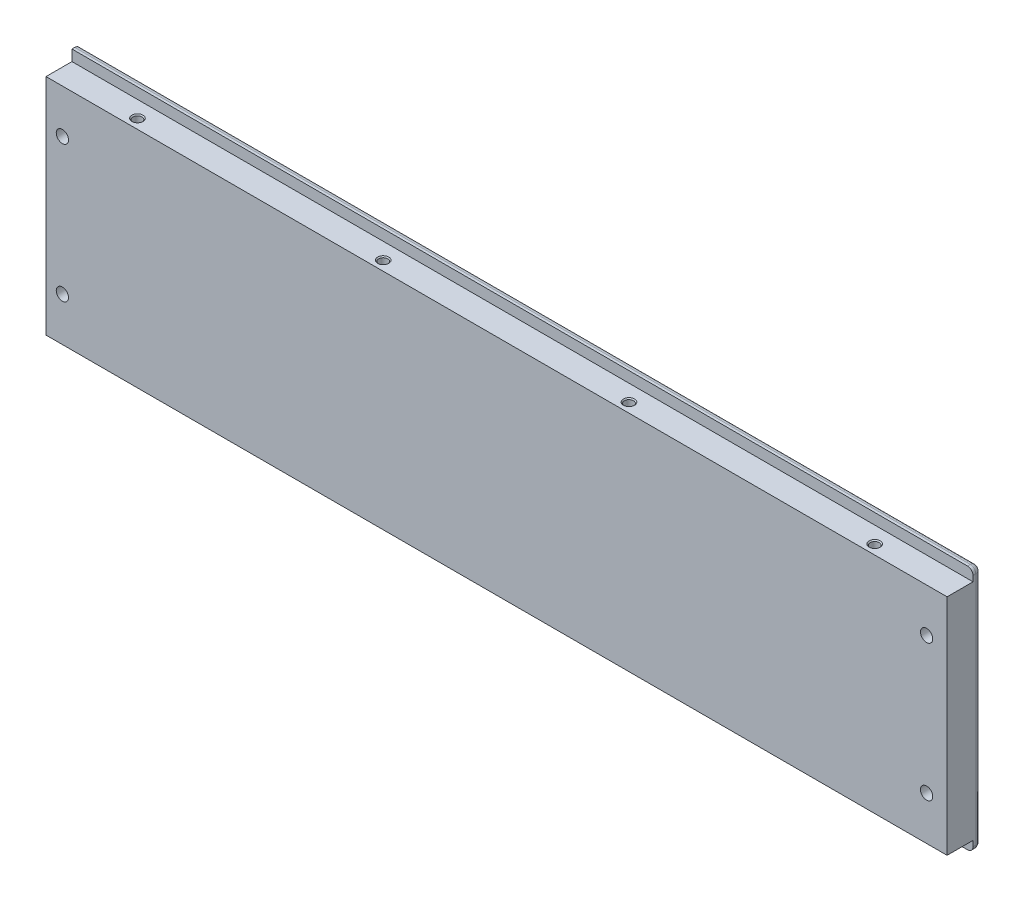
SolidWorks part; units mm, degrees
material "6061 合金"
ref_plane "前基準面" through (0, 0, 0) normal (0, 0, 1) x (1, 0, 0)
ref_plane "上基準面" through (0, 0, 0) normal (0, 1, 0) x (1, 0, 0)
ref_plane "右基準面" through (0, 0, 0) normal (1, 0, 0) x (0, 0, -1)
sketch "草圖1" plane through (0, 0, 0) normal (0, 0, 1) x (1, 0, 0)
  line L1 (0, 0) -> (330, 0)
  line L2 (0, 0) -> (0, 90)
  line L3 (0, 90) -> (330, 90)
  line L4 (330, 0) -> (330, 90)
  dimension "D1" = 330
  dimension "D2" = 90
extrude "填料-伸長1" add sketch "草圖1" along normal blind 12.5
sketch "草圖2" plane through (0, 0, 0) normal (-1, 0, 0) x (0, 0, 1)
  line L0 (0, 90) -> (0, 0) construction
  line L1 (12.5, 90) -> (3, 90)
  line L2 (12.5, 90) -> (12.5, 86)
  line L3 (12.5, 86) -> (3, 86)
  line L4 (3, 90) -> (3, 86)
  line L5 (12.5, 0) -> (3, 0)
  line L6 (12.5, 0) -> (12.5, 4)
  line L7 (12.5, 4) -> (3, 4)
  line L8 (3, 0) -> (3, 4)
  dimension "D1" = 3
  dimension "D2" = 3
  dimension "D3" = 4
  dimension "D4" = 4
extrude "除料-伸長1" cut sketch "草圖2" against normal through all
hole_wizard "M4 六角凹錐坑螺釘的錐孔1" positions "草圖4" profile "草圖3" countersink size "M4" standard "Iso" end condition through all
sketch "草圖4" plane through (0, 0, 0) normal (0, 0, -1) x (-1, 0, 0)
  line L0 (-330, 0) -> (-330, 90) construction
  line L1 (-330, 90) -> (0, 90) construction
  line L2 (0, 0) -> (-330, 0) construction
  line L3 (0, 90) -> (0, 0) construction
  point P0 (-322.5, 70)
  point P2 (-322.5, 20)
  point P4 (-6, 70)
  point P6 (-6, 20)
  dimension "D1" = 7.5
  dimension "D2" = 20
  dimension "D3" = 20
  dimension "D4" = 6
sketch "草圖3" plane through (322.5, 70, 0) normal (1, 0, 0) x (0, 1, 0)
  line L0 (0, 0) -> (0, 12.5)
  line L1 (0, 12.5) -> (2.25, 12.5)
  line L2 (2.25, 12.5) -> (2.25, 2.23)
  line L3 (2.25, 2.23) -> (4.48, 0)
  line L5 (4.48, 0) -> (0, 0)
  line L6 (-2.25, 2.23) -> (-4.48, 0) construction
  line L11 (0, -6.35) -> (0, 107.95) construction
  dimension "貫穿孔直徑" = 4.5
  dimension "貫穿孔深度" = 12.5
  dimension "近端錐孔直徑" = 8.96
  dimension "近端錐孔角度" = 90
hole_wizard "M4 螺紋孔1" positions "草圖6" profile "草圖5" tap size "M4" standard "Iso" end condition through all
sketch "草圖6" plane through (0, 86, 0) normal (0, 1, 0) x (1, 0, 0)
  line L0 (0, -3) -> (0, -12.5) construction
  line L1 (330, -3) -> (0, -3) construction
  point P0 (30, -9)
  point P2 (120, -9)
  point P4 (210, -9)
  point P6 (300, -9)
  dimension "D1" = 90
  dimension "D2" = 90
  dimension "D3" = 90
  dimension "D4" = 30
  dimension "D5" = 6
sketch "草圖5" plane through (30, 86, 9) normal (1, 0, 0) x (0, 0, 1)
  line L0 (0, 0) -> (0, 86)
  line L1 (0, 86) -> (1.65, 86)
  line L2 (1.65, 86) -> (1.65, 0.375)
  line L3 (1.65, 0.375) -> (2.025, 0)
  line L5 (2.025, 0) -> (0, 0)
  line L6 (-1.65, 0.375) -> (-2.025, 0) construction
  line L11 (0, -6.35) -> (0, 107.95) construction
  dimension "貫穿螺孔鑽直徑" = 3.3
  dimension "貫穿螺孔鑽深度" = 86
  dimension "近端錐孔直徑" = 4.05
  dimension "近端錐孔角度" = 90
cosmetic thread "鑽孔螺紋1" parameters "D2"=4
cosmetic thread "鑽孔螺紋2" parameters "D2"=4
cosmetic thread "鑽孔螺紋3" parameters "D2"=4
cosmetic thread "鑽孔螺紋4" parameters "D2"=4
fillet "圓角2" radius 2 2 edges at (330, 90, 1.5) (330, 0, 1.5)
fillet "圓角3" radius 2 3 edges at (164, 90, 0) (164, 0, 0) (330, 45, 0)
